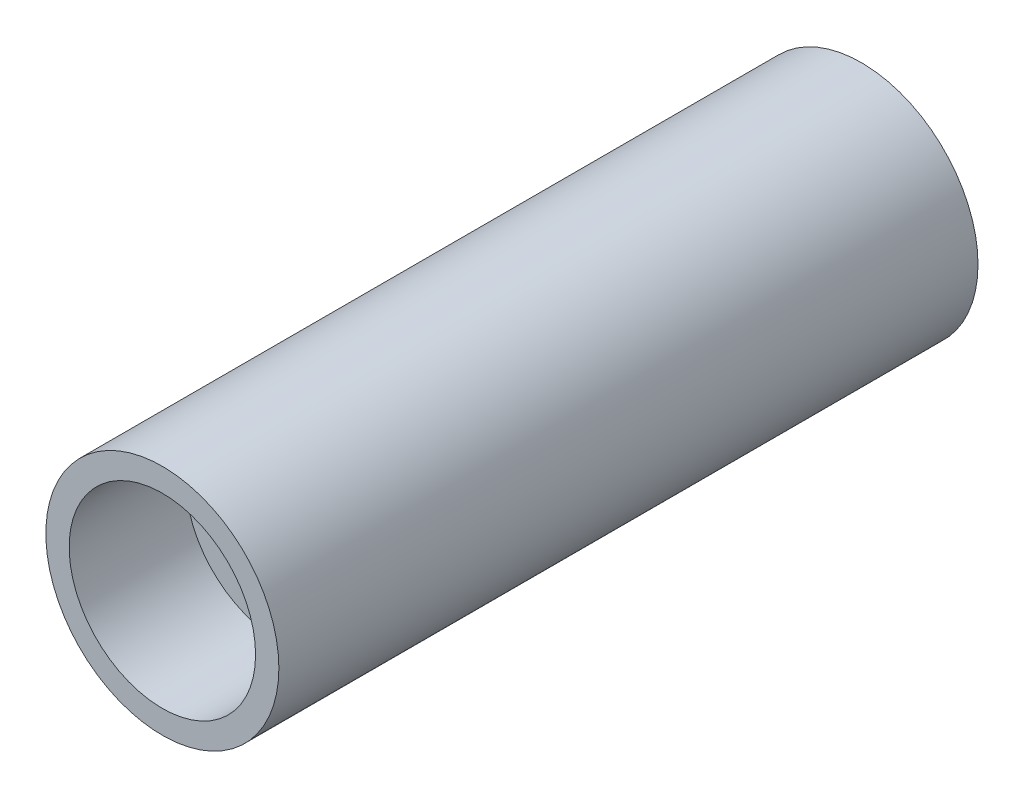
SolidWorks part; units mm, degrees
ref_plane "Front Plane" through (0, 0, 0) normal (0, 0, 1) x (1, 0, 0)
ref_plane "Top Plane" through (0, 0, 0) normal (0, 1, 0) x (1, 0, 0)
ref_plane "Right Plane" through (0, 0, 0) normal (1, 0, 0) x (0, 0, -1)
sketch "Sketch1" plane through (0, 0, 0) normal (0, 0, 1) x (1, 0, 0)
  circle A0 centre (0, 0) radius 5
  dimension "D2" = 10
extrude "Boss-Extrude1" add sketch "Sketch1" along normal blind 30
sketch "Sketch2" plane through (0, 0, 30) normal (0, 0, 1) x (1, 0, 0)
  circle A0 centre (0, 0) radius 4
  dimension "D1" = 8
extrude "Cut-Extrude1" cut sketch "Sketch2" against normal blind 5
